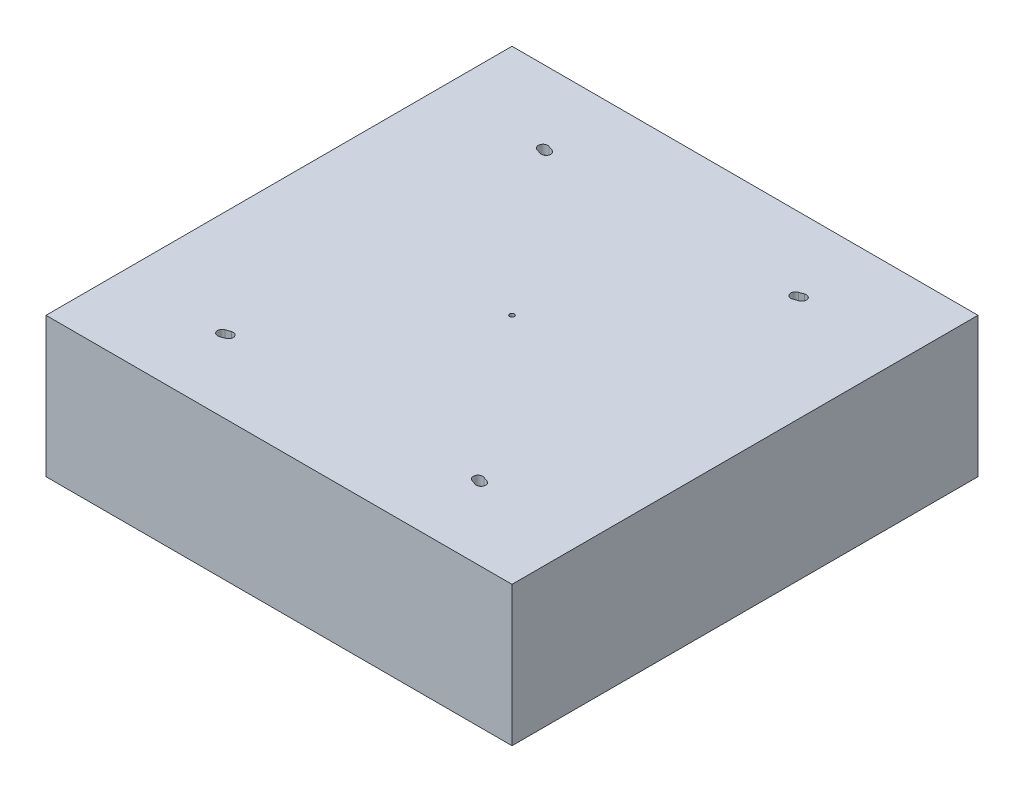
SolidWorks part; units mm, degrees
ref_plane "Front Plane" through (0, 0, 0) normal (0, 0, 1) x (1, 0, 0)
ref_plane "Top Plane" through (0, 0, 0) normal (0, 1, 0) x (1, 0, 0)
ref_plane "Right Plane" through (0, 0, 0) normal (1, 0, 0) x (0, 0, -1)
sketch "Sketch1" plane through (0, 0, 0) normal (0, 1, 0) x (1, 0, 0)
  line L0 (0, 50) -> (0, -50) construction
  line L1 (-50, 50) -> (50, 50)
  line L2 (-50, 50) -> (-50, -50)
  line L3 (-50, -50) -> (50, -50)
  line L4 (50, 50) -> (50, -50)
  line L5 (-50, 0) -> (50, 0) construction
  dimension "D1" = 50
  dimension "D2" = 50
  dimension "D3" = 50
  dimension "D4" = 50
extrude "Boss-Extrude1" add sketch "Sketch1" along normal mid plane 30
sketch "Sketch2" plane through (0, 15, 0) normal (0, 1, 0) x (1, 0, 0)
  line L0 (-41.3332, -39.0825) -> (-14.1973, -29.7389) construction
  line L1 (-50, -50) -> (50, -50) construction
  line L2 (-27.7653, -34.4107) -> (-26.7653, -34.0664) construction
  line L3 (-28.0908, -33.4652) -> (-27.0908, -33.1208)
  line L4 (-27.4397, -35.3562) -> (-26.4397, -35.0119)
  circle A0 centre (0, 0) radius 0.5
  arc A1 (-28.0908, -33.4652) -> (-27.4397, -35.3562) centre (-27.7653, -34.4107) ccw
  arc A2 (-26.4397, -35.0119) -> (-27.0908, -33.1208) centre (-26.7653, -34.0664) ccw
  point P9 (-27.2653, -34.2385)
  dimension "D2" = 1
  dimension "D4" = 1
  dimension "D1" = 19
  dimension "D3" = 1
extrude "Cut-Extrude1" cut sketch "Sketch2" against normal blind 2
mirror "Mirror1" about plane through (0, 0, 0) normal (0, 0, 1) of "Cut-Extrude1" second plane through (0, 0, 0) second plane normal (1, 0, 0)
